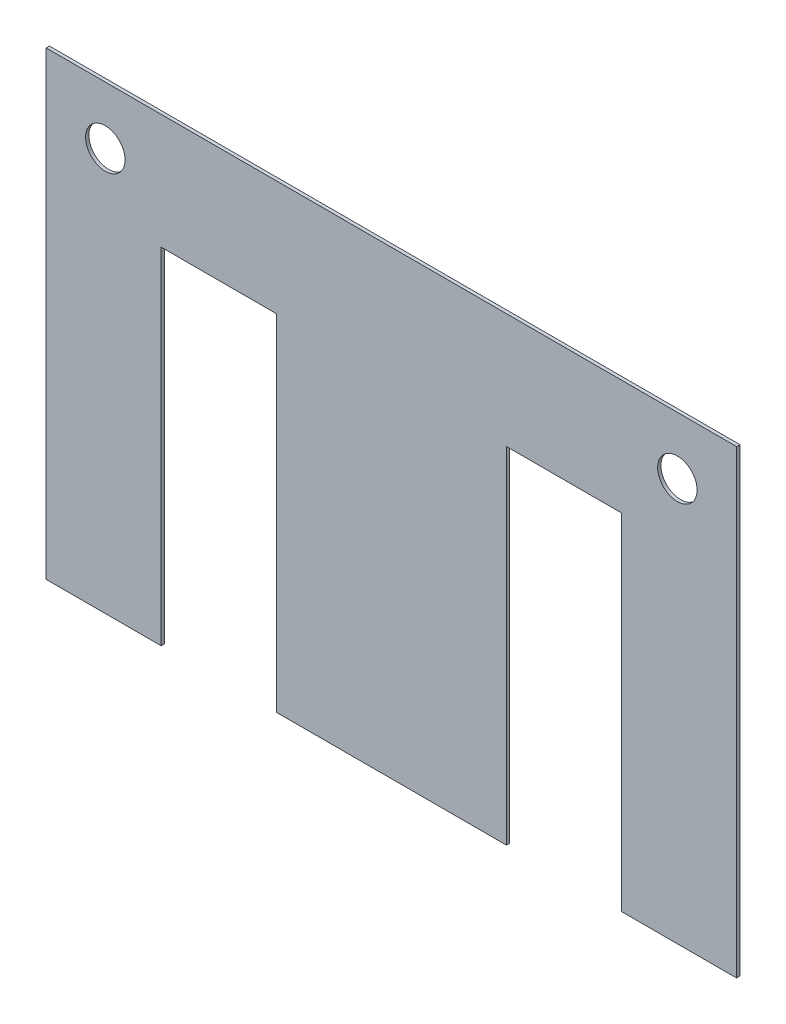
SolidWorks part; units mm, degrees
material "Chrome Stainless Steel"
ref_plane "Front Plane" through (0, 0, 0) normal (0, 0, 1) x (1, 0, 0)
ref_plane "Top Plane" through (0, 0, 0) normal (0, 1, 0) x (1, 0, 0)
ref_plane "Right Plane" through (0, 0, 0) normal (1, 0, 0) x (0, 0, -1)
sketch "Sketch1" plane through (0, 0, 0) normal (0, 0, 1) x (1, 0, 0)
  line L0 (0, 0) -> (0, 70)
  line L1 (0, 70) -> (105, 70)
  line L2 (105, 70) -> (105, 0)
  line L3 (105, 0) -> (87.5, 0)
  line L4 (87.5, 0) -> (87.5, 52.5)
  line L5 (87.5, 52.5) -> (70, 52.5)
  line L6 (70, 52.5) -> (70, 0)
  line L7 (70, 0) -> (35, 0)
  line L8 (35, 0) -> (35, 52.5)
  line L9 (35, 52.5) -> (17.5, 52.5)
  line L10 (17.5, 52.5) -> (17.5, 0)
  line L11 (17.5, 0) -> (0, 0)
  line L12 (52.5, 72.9336) -> (52.5, -3.5677) construction
  circle A0 centre (9, 61.25) radius 3
  circle A1 centre (96, 61.25) radius 3
  dimension "D7" = 6
  dimension "D8" = 6
  dimension "D1" = 105
  dimension "D2" = 70
  dimension "D3" = 17.5
  dimension "D4" = 17.5
  dimension "D5" = 35
  dimension "D6" = 52.5
  dimension "D9" = 87
  dimension "D10" = 8.75
extrude "Boss-Extrude1" add sketch "Sketch1" along normal blind 0.5
